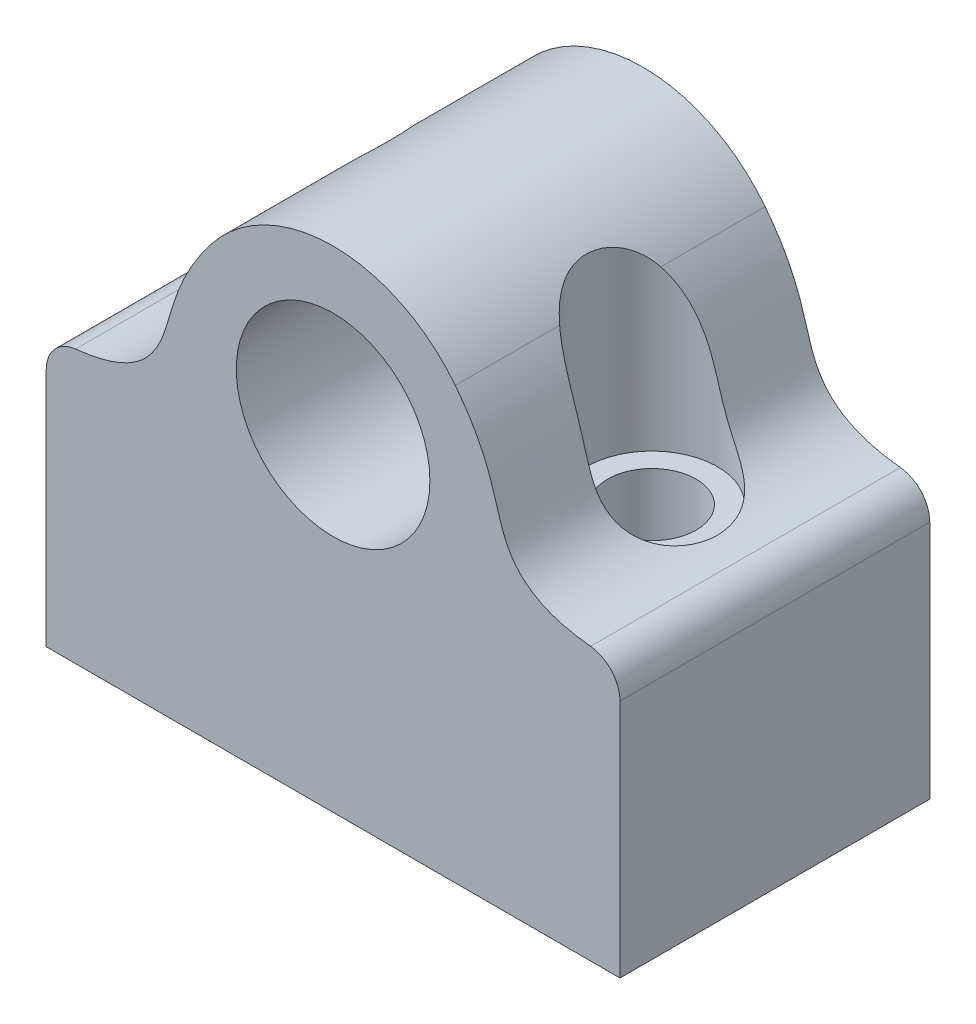
SolidWorks part; units mm, degrees
material "ABS"
ref_plane "Front Plane" through (0, 0, 0) normal (0, 0, 1) x (1, 0, 0)
ref_plane "Top Plane" through (0, 0, 0) normal (0, 1, 0) x (1, 0, 0)
ref_plane "Right Plane" through (0, 0, 0) normal (1, 0, 0) x (0, 0, -1)
sketch "Sketch1" plane through (0, 0, 0) normal (0, 0, 1) x (1, 0, 0)
  line L0 (-22.225, -5) -> (22.225, -5) construction
  line L1 (22.225, -10) -> (-22.225, -10)
  line L2 (22.225, -10) -> (22.225, -5)
  line L4 (-22.225, -10) -> (-22.225, -5)
  line L5 (0, 12) -> (0, -10) construction
  line L7 (-7.7296, 9.6049) -> (-11.2054, 5.1418) construction
  circle A0 centre (0, 0) radius 7.5
  arc A1 (9.4675, 7.3734) -> (-9.4675, 7.3734) centre (0, 0) ccw
  spline S0 degree 3 poles (-22.225, -5) (-16.6311, -4.982) (-12.3227, -1.7284) (-12.5305, 3.4404) (-9.4675, 7.3734) knots 0 0 0 0 0.501955 1 1 1 1
  spline S1 degree 3 poles (22.225, -5) (16.6311, -4.982) (12.3227, -1.7284) (12.5305, 3.4404) (9.4675, 7.3734) knots 0 0 0 0 0.501955 1 1 1 1
  dimension "D1" = 15
  dimension "D5" = 24
  dimension "D2" = 10
  dimension "D3" = 44.45
  dimension "D4" = 5
  dimension "D6" = 8.7669
extrude "Boss-Extrude1" add sketch "Sketch1" along normal mid plane 24
sketch "Sketch3" plane through (0, -10, 0) normal (0, -1, 0) x (1, 0, 0)
  line L0 (12.7, 0) -> (-12.7, 0) construction
  circle A0 centre (-12.7, 0) radius 3.425
  circle A1 centre (12.7, 0) radius 3.425
  point P3 (0, 0)
  dimension "D2" = 6.85
  dimension "D3" = 6.85
  dimension "D1" = 25.4
extrude "Cut-Extrude1" cut sketch "Sketch3" against normal through all
fillet "Fillet1" radius 2.54 2 edges at (22.225, -5, 0) (-22.225, -5, 0)
ref_plane "Plane1" through (0, -5, 0) normal (0, -1, 0) x (-1, 0, 0)
sketch "Sketch4" plane through (0, -5, 0) normal (0, -1, 0) x (-1, 0, 0)
  circle A0 centre (12.7, 0) radius 5.08
  circle A1 centre (-12.7, 0) radius 5.08
  dimension "D1" = 10.16
  dimension "D2" = 10.16
extrude "Cut-Extrude2" cut sketch "Sketch4" against normal through all
sketch "Sketch5" plane through (0, -10, 0) normal (0, -1, 0) x (1, 0, 0)
  line L4 (-22.225, -12) -> (22.225, -12)
  line L5 (22.225, -12) -> (22.225, 12)
  line L6 (22.225, 12) -> (-22.225, 12)
  line L7 (22.225, -12) -> (22.225, 12)
  line L8 (-22.225, -12) -> (22.225, -12)
  line L9 (-22.225, 12) -> (-22.225, -12)
  line L10 (22.225, 12) -> (-22.225, 12)
  line L11 (-22.225, 12) -> (-22.225, -12)
  circle A0 centre (12.7, 0) radius 3.425 construction
  circle A1 centre (-12.7, 0) radius 3.425 construction
  circle A2 centre (12.7, 0) radius 3.425
  circle A3 centre (-12.7, 0) radius 3.425
  dimension "D1" = 0
extrude "Boss-Extrude2" add sketch "Sketch5" along normal blind 16
